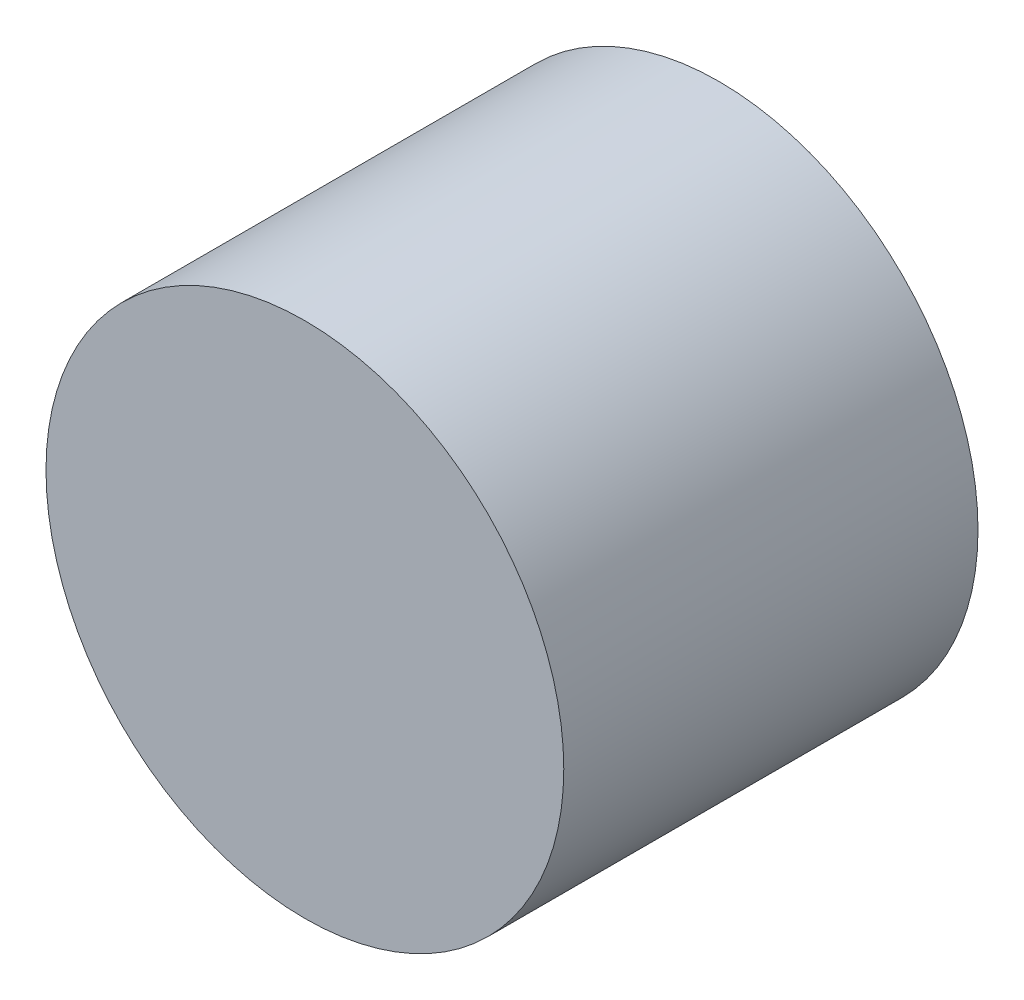
SolidWorks part; units mm, degrees
ref_plane "Front Plane" through (0, 0, 0) normal (0, 0, 1) x (1, 0, 0)
ref_plane "Top Plane" through (0, 0, 0) normal (0, 1, 0) x (1, 0, 0)
ref_plane "Right Plane" through (0, 0, 0) normal (1, 0, 0) x (0, 0, -1)
sketch "Sketch1" plane through (0, 0, 0) normal (0, 0, 1) x (1, 0, 0)
  circle A0 centre (0, 0) radius 2.5
  dimension "D1" = 5
extrude "Boss-Extrude1" add sketch "Sketch1" along normal blind 4 contours A0
